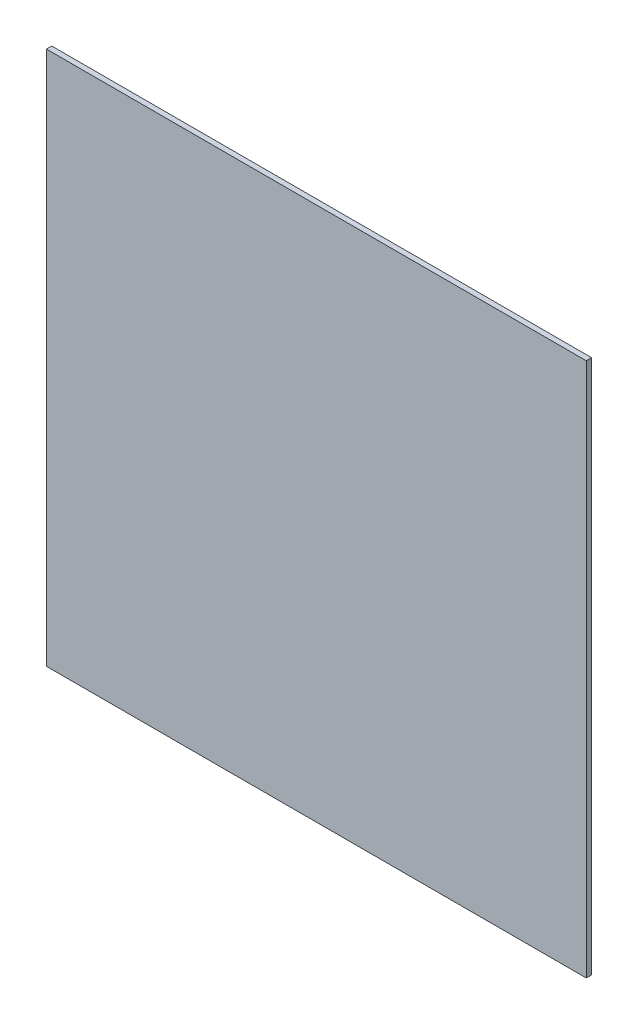
SolidWorks part; units mm, degrees
material "Acrílico (Impacto medio-alto)"
ref_plane "Alzado" through (0, 0, 0) normal (0, 0, 1) x (1, 0, 0)
ref_plane "Planta" through (0, 0, 0) normal (0, 1, 0) x (1, 0, 0)
ref_plane "Vista lateral" through (0, 0, 0) normal (1, 0, 0) x (0, 0, -1)
sketch "Croquis1" plane through (0, 0, 0) normal (0, 0, 1) x (1, 0, 0)
  line L1 (0, 0) -> (305, 0)
  line L2 (0, 0) -> (0, 302)
  line L3 (0, 302) -> (305, 302)
  line L4 (305, 0) -> (305, 302)
  dimension "D1" = 302
  dimension "D2" = 305
extrude "Saliente-Extruir1" add sketch "Croquis1" along normal blind 3
